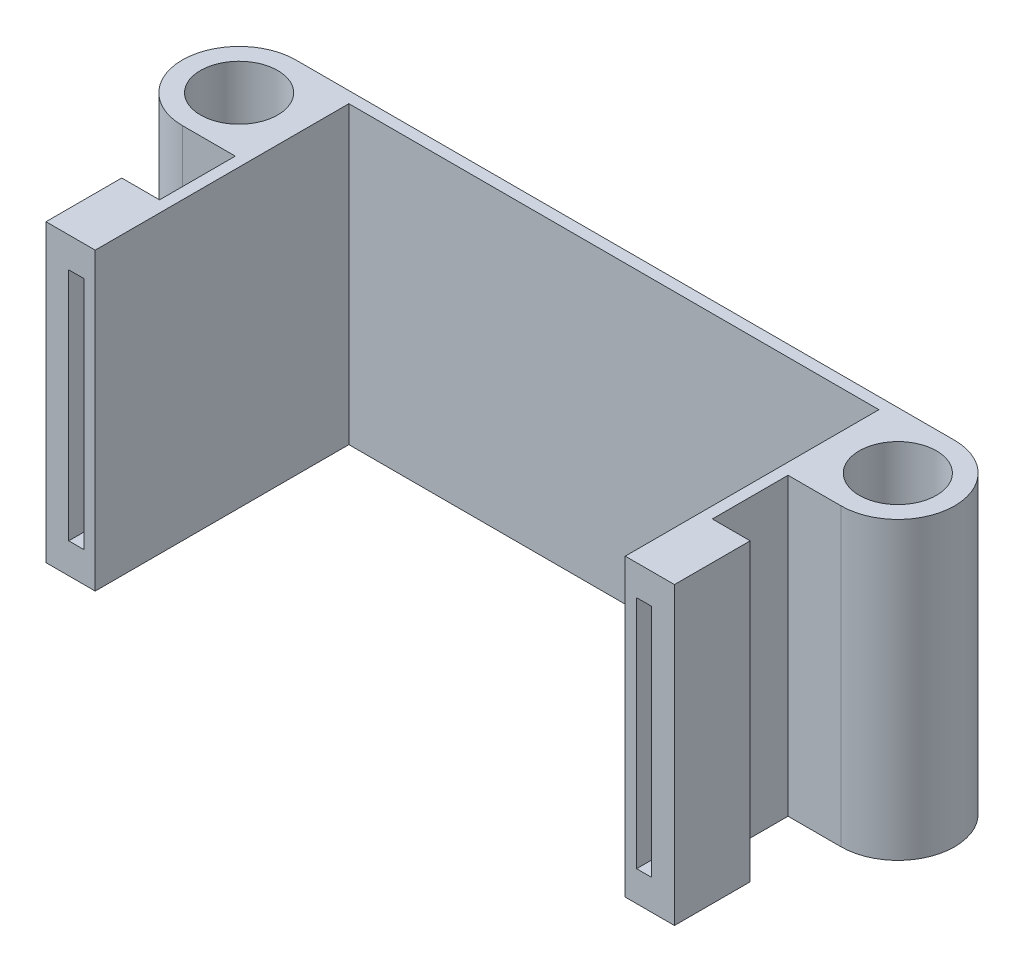
SolidWorks part; units mm, degrees
ref_plane "Front Plane" through (0, 0, 0) normal (0, 0, 1) x (1, 0, 0)
ref_plane "Top Plane" through (0, 0, 0) normal (0, 1, 0) x (1, 0, 0)
ref_plane "Right Plane" through (0, 0, 0) normal (1, 0, 0) x (0, 0, -1)
sketch "Sketch1" plane through (0, 0, 0) normal (0, 1, 0) x (1, 0, 0)
  line L0 (0, 3.75) -> (43.5, 3.75)
  line L1 (3.5, -3.75) -> (0, -3.75)
  line L2 (39.25, 3) -> (39.25, -13.75)
  line L3 (3.5, -13.75) -> (1, -13.75)
  line L4 (3.5, -3.75) -> (3.5, -13.75)
  line L5 (3.5, -13.75) -> (4.25, -13.75)
  line L6 (40, -3.75) -> (40, -13.75)
  line L7 (40, -13.75) -> (39.25, -13.75)
  line L8 (40, -3.75) -> (43.5, -3.75)
  line L12 (4.25, 3) -> (4.25, -13.75)
  line L13 (1, -13.75) -> (1, -8.75)
  line L14 (1, -8.75) -> (3.5, -8.75)
  line L15 (21.75, 3.75) -> (21.75, 3)
  line L18 (40, -13.75) -> (42.5, -13.75)
  line L19 (42.5, -13.75) -> (42.5, -8.75)
  line L20 (42.5, -8.75) -> (40, -8.75)
  line L21 (4.25, 3) -> (39.25, 3)
  circle A0 centre (0, 0) radius 2.55
  circle A1 centre (43.5, 0) radius 2.55
  circle A4 centre (0, 0) radius 3.75
  circle A5 centre (43.5, 0) radius 3.75
  dimension "D1" = 5.1
  dimension "D3" = 7.5
  dimension "D2" = 43.5
  dimension "D4" = 0.75
  dimension "D5" = 0.75
  dimension "D6" = 35
  dimension "D10" = 2.5
  dimension "D11" = 5
  dimension "D12" = 5
extrude "Boss-Extrude2" add sketch "Sketch1" along normal blind 19.5
sketch "Sketch2" plane through (0, 0, 13.75) normal (0, 0, 1) x (1, 0, 0)
  line L1 (3.5, 17.5) -> (2.5, 17.5)
  line L2 (3.5, 17.5) -> (3.5, 2)
  line L3 (3.5, 2) -> (2.5, 2)
  line L4 (2.5, 17.5) -> (2.5, 2)
  line L5 (41, 17.5) -> (40, 17.5)
  line L6 (41, 17.5) -> (41, 2)
  line L7 (41, 2) -> (40, 2)
  line L8 (40, 17.5) -> (40, 2)
  line L9 (39.25, 19.5) -> (39.25, 0) construction
  line L10 (4.25, 19.5) -> (1, 19.5) construction
  line L11 (42.5, 19.5) -> (39.25, 19.5) construction
  line L12 (4.25, 19.5) -> (4.25, 0) construction
  point P18 (4.5, 10.3159)
  dimension "D1" = 0.75
  dimension "D2" = 0.75
  dimension "D3" = 2
  dimension "D4" = 2
  dimension "D5" = 1
  dimension "D6" = 15.5
extrude "Cut-Extrude1" cut sketch "Sketch2" against normal up to surface (5 mm away) up to face at (2.25, 9.75, 8.75)
